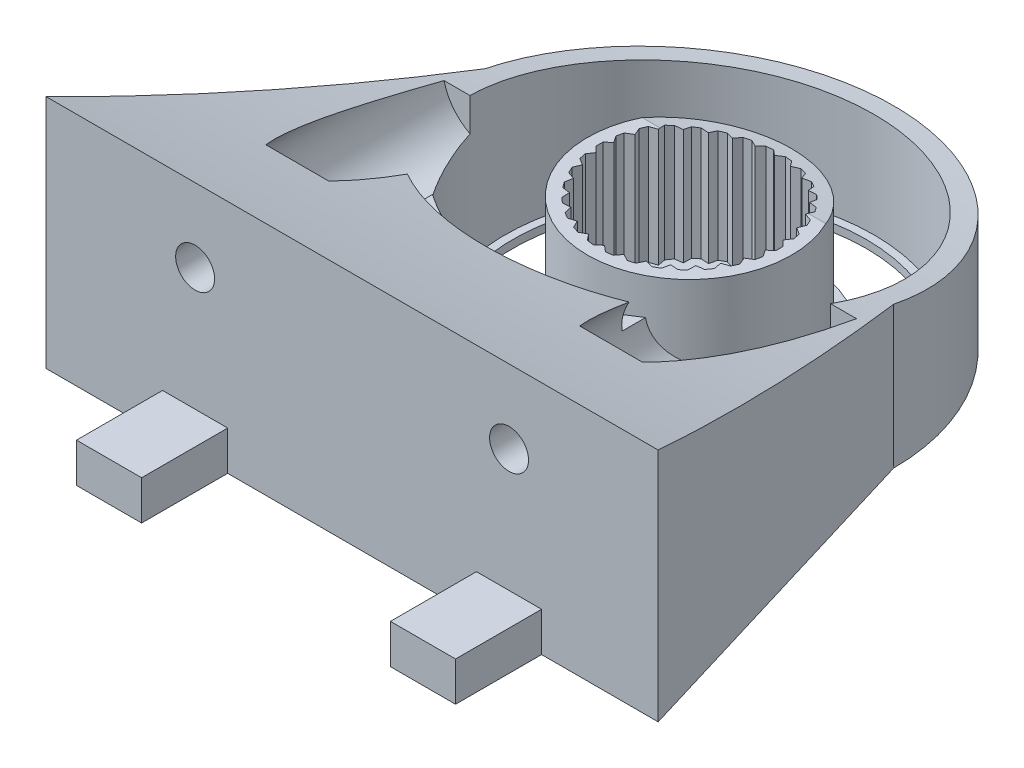
SolidWorks part; units mm, degrees
ref_plane "Front Plane" through (0, 0, 0) normal (0, 0, 1) x (1, 0, 0)
ref_plane "Top Plane" through (0, 0, 0) normal (0, 1, 0) x (1, 0, 0)
ref_plane "Right Plane" through (0, 0, 0) normal (1, 0, 0) x (0, 0, -1)
sketch "Sketch1" plane through (0, 0, 0) normal (0, 1, 0) x (1, 0, 0)
  line L208 (0, 27.1182) -> (0, 42.0182) construction
  line L209 (0, 57.7182) -> (-47.2537, 57.7182) construction
  line L210 (16.6412, 0.931) -> (17.2272, 1.5169) construction
  line L211 (14.3988, 4.3454) -> (13.8128, 3.7594) construction
  line L212 (13.8128, 10.4769) -> (14.3988, 9.891) construction
  line L213 (17.2272, 12.7194) -> (16.6412, 13.3054) construction
  line L214 (23.3588, 13.3054) -> (22.7728, 12.7194) construction
  line L215 (25.6012, 9.891) -> (26.1872, 10.4769) construction
  line L216 (26.1872, 3.7594) -> (25.6012, 4.3454) construction
  line L217 (22.7728, 1.5169) -> (23.3588, 0.931) construction
  line L218 (-29.6, -20.9818) -> (-29.6, -4.7818) construction
  line L219 (-38, -20.9818) -> (-29.6, -20.9818) construction
  line L220 (-38, -4.7818) -> (-38, -20.9818) construction
  line L221 (-29.6, -4.7818) -> (-38, -4.7818) construction
  line L222 (-23.3588, 0.931) -> (-22.7728, 1.5169) construction
  line L223 (-25.6012, 4.3454) -> (-26.1872, 3.7594) construction
  line L224 (-26.1872, 10.4769) -> (-25.6012, 9.891) construction
  line L225 (-22.7728, 12.7194) -> (-23.3588, 13.3054) construction
  line L226 (-16.6412, 13.3054) -> (-17.2272, 12.7194) construction
  line L227 (-14.3988, 9.891) -> (-13.8128, 10.4769) construction
  line L228 (-13.8128, 3.7594) -> (-14.3988, 4.3454) construction
  line L229 (-17.2272, 1.5169) -> (-16.6412, 0.931) construction
  line L230 (23.3588, -26.6946) -> (22.7728, -27.2806) construction
  line L231 (25.6012, -30.109) -> (26.1872, -29.5231) construction
  line L232 (26.1872, -36.2406) -> (25.6012, -35.6546) construction
  line L233 (22.7728, -38.4831) -> (23.3588, -39.069) construction
  line L234 (16.6412, -39.069) -> (17.2272, -38.4831) construction
  line L235 (14.3988, -35.6546) -> (13.8128, -36.2406) construction
  line L236 (13.8128, -29.5231) -> (14.3988, -30.109) construction
  line L237 (17.2272, -27.2806) -> (16.6412, -26.6946) construction
  line L238 (-31.2, -44.0818) -> (-38.4, -44.0818) construction
  line L239 (-31.2, -51.2818) -> (-31.2, -44.0818) construction
  line L240 (-38.4, -51.2818) -> (-31.2, -51.2818) construction
  line L241 (-38.4, -44.0818) -> (-38.4, -51.2818) construction
  line L242 (-16.6412, -26.6946) -> (-17.2272, -27.2806) construction
  line L243 (-14.3988, -30.109) -> (-13.8128, -29.5231) construction
  line L244 (-13.8128, -36.2406) -> (-14.3988, -35.6546) construction
  line L245 (-17.2272, -38.4831) -> (-16.6412, -39.069) construction
  line L246 (-23.3588, -39.069) -> (-22.7728, -38.4831) construction
  line L247 (-25.6012, -35.6546) -> (-26.1872, -36.2406) construction
  line L248 (-26.1872, -29.5231) -> (-25.6012, -30.109) construction
  line L249 (-22.7728, -27.2806) -> (-23.3588, -26.6946) construction
  line L250 (-38.4, 18.3182) -> (-31.2, 18.3182) construction
  line L251 (-38.4, 25.5182) -> (-38.4, 18.3182) construction
  line L252 (-31.2, 25.5182) -> (-38.4, 25.5182) construction
  line L253 (-31.2, 18.3182) -> (-31.2, 25.5182) construction
  line L254 (38.4, -44.0818) -> (31.2, -44.0818) construction
  line L255 (38.4, -51.2818) -> (38.4, -44.0818) construction
  line L256 (31.2, -51.2818) -> (38.4, -51.2818) construction
  line L257 (31.2, -44.0818) -> (31.2, -51.2818) construction
  line L258 (31.2, 18.3182) -> (38.4, 18.3182) construction
  line L259 (31.2, 25.5182) -> (31.2, 18.3182) construction
  line L260 (38.4, 25.5182) -> (31.2, 25.5182) construction
  line L261 (38.4, 18.3182) -> (38.4, 25.5182) construction
  line L262 (-8.1, 25.1182) -> (-8.1, 16.7182) construction
  line L263 (8.1, 25.1182) -> (-8.1, 25.1182) construction
  line L264 (8.1, 16.7182) -> (8.1, 25.1182) construction
  line L265 (-8.1, 16.7182) -> (8.1, 16.7182) construction
  line L266 (11.2, -37.6818) -> (11.2, -28.0818) construction
  line L267 (-9.2, -39.6818) -> (9.2, -39.6818) construction
  line L268 (-11.2, -28.0818) -> (-11.2, -37.6818) construction
  line L269 (-24.8, -24.0818) -> (-15.2, -24.0818) construction
  line L270 (-26.8, -3.6818) -> (-26.8, -22.0818) construction
  line L271 (-15.2, -1.6818) -> (-24.8, -1.6818) construction
  line L272 (-11.2, 11.9182) -> (-11.2, 2.3182) construction
  line L273 (9.2, 13.9182) -> (-9.2, 13.9182) construction
  line L274 (11.2, 2.3182) -> (11.2, 11.9182) construction
  line L275 (24.8, -1.6818) -> (15.2, -1.6818) construction
  line L276 (26.8, -22.0818) -> (26.8, -3.6818) construction
  line L277 (15.2, -24.0818) -> (24.8, -24.0818) construction
  line L278 (8.1, -42.4818) -> (-8.1, -42.4818) construction
  line L279 (8.1, -50.8818) -> (8.1, -42.4818) construction
  line L280 (-8.1, -50.8818) -> (8.1, -50.8818) construction
  line L281 (-8.1, -42.4818) -> (-8.1, -50.8818) construction
  line L282 (29.6, -4.7818) -> (29.6, -20.9818) construction
  line L283 (38, -4.7818) -> (29.6, -4.7818) construction
  line L284 (38, -20.9818) -> (38, -4.7818) construction
  line L285 (29.6, -20.9818) -> (38, -20.9818) construction
  line L286 (40, -51.8818) -> (40, -38.1318) construction
  line L287 (40, -38.1318) -> (39, -37.1318) construction
  line L288 (39, -37.1318) -> (36, -37.1318) construction
  line L289 (36, -37.1318) -> (36, -40.1318) construction
  line L290 (36, -40.1318) -> (37.6041, -40.1318) construction
  line L291 (38.0965, -40.7186) -> (37.9168, -41.7381) construction
  line L292 (37.0304, -42.4818) -> (32.3339, -42.4818) construction
  line L293 (30.2125, -41.6031) -> (29.6787, -41.0693) construction
  line L294 (28.8, -38.9479) -> (28.8, -26.8157) construction
  line L295 (29.6787, -24.6944) -> (30.2125, -24.1605) construction
  line L296 (32.3339, -23.2818) -> (37.0304, -23.2818) construction
  line L297 (37.9168, -24.0255) -> (38.0965, -25.045) construction
  line L298 (37.6041, -25.6318) -> (36, -25.6318) construction
  line L299 (36, -25.6318) -> (36, -28.6318) construction
  line L300 (36, -28.6318) -> (39, -28.6318) construction
  line L301 (39, -28.6318) -> (40, -27.6318) construction
  line L302 (40, -27.6318) -> (40, 1.8682) construction
  line L303 (40, 1.8682) -> (39, 2.8682) construction
  line L304 (39, 2.8682) -> (36, 2.8682) construction
  line L305 (36, 2.8682) -> (36, -0.1318) construction
  line L306 (36, -0.1318) -> (37.6041, -0.1318) construction
  line L307 (38.0965, -0.7186) -> (37.9168, -1.7381) construction
  line L308 (37.0304, -2.4818) -> (32.3339, -2.4818) construction
  line L309 (30.2125, -1.6031) -> (29.6787, -1.0693) construction
  line L310 (28.8, 1.0521) -> (28.8, 13.1843) construction
  line L311 (29.6787, 15.3056) -> (30.2125, 15.8395) construction
  line L312 (32.3339, 16.7182) -> (37.0304, 16.7182) construction
  line L313 (37.9168, 15.9745) -> (38.0965, 14.955) construction
  line L314 (37.6041, 14.3682) -> (36, 14.3682) construction
  line L315 (36, 14.3682) -> (36, 11.3682) construction
  line L316 (36, 11.3682) -> (39, 11.3682) construction
  line L317 (39, 11.3682) -> (40, 12.3682) construction
  line L318 (40, 12.3682) -> (40, 26.1182) construction
  line L319 (39, 27.1182) -> (25.25, 27.1182) construction
  line L320 (25.25, 27.1182) -> (24.25, 26.1182) construction
  line L321 (24.25, 26.1182) -> (24.25, 23.1182) construction
  line L322 (24.25, 23.1182) -> (27.25, 23.1182) construction
  line L323 (27.25, 23.1182) -> (27.25, 24.7223) construction
  line L324 (27.8368, 25.2147) -> (28.8563, 25.035) construction
  line L325 (29.6, 24.1486) -> (29.6, 19.4521) construction
  line L326 (28.7213, 17.3307) -> (28.1875, 16.7969) construction
  line L327 (26.0661, 15.9182) -> (13.9339, 15.9182) construction
  line L328 (11.8125, 16.7969) -> (11.2787, 17.3307) construction
  line L329 (10.4, 19.4521) -> (10.4, 24.1486) construction
  line L330 (11.1437, 25.035) -> (12.1632, 25.2147) construction
  line L331 (12.75, 24.7223) -> (12.75, 23.1182) construction
  line L332 (12.75, 23.1182) -> (15.75, 23.1182) construction
  line L333 (15.75, 23.1182) -> (15.75, 26.1182) construction
  line L334 (15.75, 26.1182) -> (14.75, 27.1182) construction
  line L335 (14.75, 27.1182) -> (-14.75, 27.1182) construction
  line L336 (-14.75, 27.1182) -> (-15.75, 26.1182) construction
  line L337 (-15.75, 26.1182) -> (-15.75, 23.1182) construction
  line L338 (-15.75, 23.1182) -> (-12.75, 23.1182) construction
  line L339 (-12.75, 23.1182) -> (-12.75, 24.7223) construction
  line L340 (-12.1632, 25.2147) -> (-11.1437, 25.035) construction
  line L341 (-10.4, 24.1486) -> (-10.4, 19.4521) construction
  line L342 (-11.2787, 17.3307) -> (-11.8125, 16.7969) construction
  line L343 (-13.9339, 15.9182) -> (-26.0661, 15.9182) construction
  line L344 (-28.1875, 16.7969) -> (-28.7213, 17.3307) construction
  line L345 (-29.6, 19.4521) -> (-29.6, 24.1486) construction
  line L346 (-28.8563, 25.035) -> (-27.8368, 25.2147) construction
  line L347 (-27.25, 24.7223) -> (-27.25, 23.1182) construction
  line L348 (-27.25, 23.1182) -> (-24.25, 23.1182) construction
  line L349 (-24.25, 23.1182) -> (-24.25, 26.1182) construction
  line L350 (-24.25, 26.1182) -> (-25.25, 27.1182) construction
  line L351 (-25.25, 27.1182) -> (-39, 27.1182) construction
  line L352 (-40, 26.1182) -> (-40, 12.3682) construction
  line L353 (-40, 12.3682) -> (-39, 11.3682) construction
  line L354 (-39, 11.3682) -> (-36, 11.3682) construction
  line L355 (-36, 11.3682) -> (-36, 14.3682) construction
  line L356 (-36, 14.3682) -> (-37.6041, 14.3682) construction
  line L357 (-38.0965, 14.955) -> (-37.9168, 15.9745) construction
  line L358 (-37.0304, 16.7182) -> (-32.3339, 16.7182) construction
  line L359 (-30.2125, 15.8395) -> (-29.6787, 15.3056) construction
  line L360 (-28.8, 13.1843) -> (-28.8, 1.0521) construction
  line L361 (-29.6787, -1.0693) -> (-30.2125, -1.6031) construction
  line L362 (-32.3339, -2.4818) -> (-37.0304, -2.4818) construction
  line L363 (-37.9168, -1.7381) -> (-38.0965, -0.7186) construction
  line L364 (-37.6041, -0.1318) -> (-36, -0.1318) construction
  line L365 (-36, -0.1318) -> (-36, 2.8682) construction
  line L366 (-36, 2.8682) -> (-39, 2.8682) construction
  line L367 (-39, 2.8682) -> (-40, 1.8682) construction
  line L368 (-40, 1.8682) -> (-40, -27.6318) construction
  line L369 (-40, -27.6318) -> (-39, -28.6318) construction
  line L370 (-39, -28.6318) -> (-36, -28.6318) construction
  line L371 (-36, -28.6318) -> (-36, -25.6318) construction
  line L372 (-36, -25.6318) -> (-37.6041, -25.6318) construction
  line L373 (-38.0965, -25.045) -> (-37.9168, -24.0255) construction
  line L374 (-37.0304, -23.2818) -> (-32.3339, -23.2818) construction
  line L375 (-30.2125, -24.1605) -> (-29.6787, -24.6944) construction
  line L376 (-28.8, -26.8157) -> (-28.8, -38.9479) construction
  line L377 (-29.6787, -41.0693) -> (-30.2125, -41.6031) construction
  line L378 (-32.3339, -42.4818) -> (-37.0304, -42.4818) construction
  line L379 (-37.9168, -41.7381) -> (-38.0965, -40.7186) construction
  line L380 (-37.6041, -40.1318) -> (-36, -40.1318) construction
  line L381 (-36, -40.1318) -> (-36, -37.1318) construction
  line L382 (-36, -37.1318) -> (-39, -37.1318) construction
  line L383 (-39, -37.1318) -> (-40, -38.1318) construction
  line L384 (-40, -38.1318) -> (-40, -51.8818) construction
  line L385 (-39, -52.8818) -> (-25.25, -52.8818) construction
  line L386 (-25.25, -52.8818) -> (-24.25, -51.8818) construction
  line L387 (-24.25, -51.8818) -> (-24.25, -48.8818) construction
  line L388 (-24.25, -48.8818) -> (-27.25, -48.8818) construction
  line L389 (-27.25, -48.8818) -> (-27.25, -50.4859) construction
  line L390 (-27.8368, -50.9783) -> (-28.8563, -50.7986) construction
  line L391 (-29.6, -49.9123) -> (-29.6, -45.2157) construction
  line L392 (-28.7213, -43.0944) -> (-28.1875, -42.5605) construction
  line L393 (-26.0661, -41.6818) -> (-13.9339, -41.6818) construction
  line L394 (-11.8125, -42.5605) -> (-11.2787, -43.0944) construction
  line L395 (-10.4, -45.2157) -> (-10.4, -49.9123) construction
  line L396 (-11.1437, -50.7986) -> (-12.1632, -50.9783) construction
  line L397 (-12.75, -50.4859) -> (-12.75, -48.8818) construction
  line L398 (-12.75, -48.8818) -> (-15.75, -48.8818) construction
  line L399 (-15.75, -48.8818) -> (-15.75, -51.8818) construction
  line L400 (-15.75, -51.8818) -> (-14.75, -52.8818) construction
  line L401 (-14.75, -52.8818) -> (14.75, -52.8818) construction
  line L402 (14.75, -52.8818) -> (15.75, -51.8818) construction
  line L403 (15.75, -51.8818) -> (15.75, -48.8818) construction
  line L404 (15.75, -48.8818) -> (12.75, -48.8818) construction
  line L405 (12.75, -48.8818) -> (12.75, -50.4859) construction
  line L406 (12.1632, -50.9783) -> (11.1437, -50.7986) construction
  line L407 (10.4, -49.9123) -> (10.4, -45.2157) construction
  line L408 (11.2787, -43.0944) -> (11.8125, -42.5605) construction
  line L409 (13.9339, -41.6818) -> (26.0661, -41.6818) construction
  line L410 (28.1875, -42.5605) -> (28.7213, -43.0944) construction
  line L411 (29.6, -45.2157) -> (29.6, -49.9123) construction
  line L412 (28.8563, -50.7986) -> (27.8368, -50.9783) construction
  line L413 (27.25, -50.4859) -> (27.25, -48.8818) construction
  line L414 (27.25, -48.8818) -> (24.25, -48.8818) construction
  line L415 (24.25, -48.8818) -> (24.25, -51.8818) construction
  line L416 (24.25, -51.8818) -> (25.25, -52.8818) construction
  line L417 (25.25, -52.8818) -> (39, -52.8818) construction
  line L418 (0, 82.2765) -> (0, 80.95) construction
  line L419 (0, 80.95) -> (-0.7581, 81.5932)
  line L420 (0, 80.95) -> (0.7581, 81.5932)
  line L421 (2.2521, 80.7133) -> (1.6443, 81.5)
  line L422 (2.2521, 80.7133) -> (3.1273, 81.1848)
  line L423 (4.4057, 80.0136) -> (3.9748, 80.9094)
  line L424 (4.4057, 80.0136) -> (5.3598, 80.2928)
  line L425 (6.3668, 78.8813) -> (6.1315, 79.8472)
  line L426 (6.3668, 78.8813) -> (7.3581, 78.9561)
  line L427 (8.0496, 77.3661) -> (8.0203, 78.3598)
  line L428 (8.0496, 77.3661) -> (9.0348, 77.2331)
  line L429 (9.3806, 75.5341) -> (9.5586, 76.5122)
  line L430 (9.3806, 75.5341) -> (10.3167, 75.1992)
  line L431 (10.3017, 73.4654) -> (10.6791, 74.3851)
  line L432 (10.3017, 73.4654) -> (11.1476, 72.9432)
  line L433 (10.7725, 71.2504) -> (11.3329, 72.0716)
  line L434 (10.7725, 71.2504) -> (11.4914, 70.5637)
  line L435 (10.7725, 68.986) -> (11.4914, 69.6726)
  line L436 (10.7725, 68.986) -> (11.3329, 68.1648)
  line L437 (10.3017, 66.771) -> (11.1476, 67.2932)
  line L438 (10.3017, 66.771) -> (10.6791, 65.8513)
  line L439 (9.3806, 64.7023) -> (10.3167, 65.0372)
  line L440 (9.3806, 64.7023) -> (9.5586, 63.7242)
  line L441 (8.0496, 62.8703) -> (9.0348, 63.0033)
  line L442 (8.0496, 62.8703) -> (8.0203, 61.8766)
  line L443 (6.3668, 61.3551) -> (7.3581, 61.2803)
  line L444 (6.3668, 61.3551) -> (6.1315, 60.3891)
  line L445 (4.4057, 60.2228) -> (5.3598, 59.9436)
  line L446 (4.4057, 60.2228) -> (3.9748, 59.3269)
  line L447 (2.2521, 59.5231) -> (3.1273, 59.0516)
  line L448 (2.2521, 59.5231) -> (1.6443, 58.7363)
  line L449 (0, 59.2864) -> (0.7581, 58.6432)
  line L450 (0, 59.2864) -> (-0.7581, 58.6432)
  line L451 (-2.2521, 59.5231) -> (-1.6443, 58.7363)
  line L452 (-2.2521, 59.5231) -> (-3.1273, 59.0516)
  line L453 (-4.4057, 60.2228) -> (-3.9748, 59.3269)
  line L454 (-4.4057, 60.2228) -> (-5.3598, 59.9436)
  line L455 (-6.3668, 61.3551) -> (-6.1315, 60.3891)
  line L456 (-6.3668, 61.3551) -> (-7.3581, 61.2803)
  line L457 (-8.0496, 62.8703) -> (-8.0203, 61.8766)
  line L458 (-8.0496, 62.8703) -> (-9.0348, 63.0033)
  line L459 (-9.3806, 64.7023) -> (-9.5586, 63.7242)
  line L460 (-9.3806, 64.7023) -> (-10.3167, 65.0372)
  line L461 (-10.3017, 66.771) -> (-10.6791, 65.8513)
  line L462 (-10.3017, 66.771) -> (-11.1476, 67.2932)
  line L463 (-10.7725, 68.986) -> (-11.3329, 68.1648)
  line L464 (-10.7725, 68.986) -> (-11.4914, 69.6726)
  line L465 (-10.7725, 71.2504) -> (-11.4914, 70.5637)
  line L466 (-10.7725, 71.2504) -> (-11.3329, 72.0716)
  line L467 (-10.3017, 73.4654) -> (-11.1476, 72.9432)
  line L468 (-10.3017, 73.4654) -> (-10.6791, 74.3851)
  line L469 (-9.3806, 75.5341) -> (-10.3167, 75.1992)
  line L470 (-9.3806, 75.5341) -> (-9.5586, 76.5122)
  line L471 (-8.0496, 77.3661) -> (-9.0348, 77.2331)
  line L472 (-8.0496, 77.3661) -> (-8.0203, 78.3598)
  line L473 (-6.3668, 78.8813) -> (-7.3581, 78.9561)
  line L474 (-6.3668, 78.8813) -> (-6.1315, 79.8472)
  line L475 (-4.4057, 80.0136) -> (-5.3598, 80.2928)
  line L476 (-4.4057, 80.0136) -> (-3.9748, 80.9094)
  line L477 (-2.2521, 80.7133) -> (-3.1273, 81.1848)
  line L478 (-2.2521, 80.7133) -> (-1.6443, 81.5)
  line L479 (0, 57.1182) -> (0, 70.1182) construction
  circle A112 centre (0, 70.1182) radius 12.4 construction
  circle A114 centre (0, 70.1182) radius 13
  arc A121 (17.2272, 1.5169) -> (22.7728, 1.5169) centre (20, 7.1182) ccw construction
  arc A122 (13.8128, 3.7594) -> (16.6412, 0.931) centre (15.227, 2.3452) ccw construction
  arc A123 (14.3988, 9.891) -> (14.3988, 4.3454) centre (20, 7.1182) ccw construction
  arc A124 (16.6412, 13.3054) -> (13.8128, 10.4769) centre (15.227, 11.8912) ccw construction
  arc A125 (22.7728, 12.7194) -> (17.2272, 12.7194) centre (20, 7.1182) ccw construction
  arc A126 (26.1872, 10.4769) -> (23.3588, 13.3054) centre (24.773, 11.8912) ccw construction
  arc A127 (25.6012, 4.3454) -> (25.6012, 9.891) centre (20, 7.1182) ccw construction
  arc A128 (23.3588, 0.931) -> (26.1872, 3.7594) centre (24.773, 2.3452) ccw construction
  arc A129 (-22.7728, 1.5169) -> (-17.2272, 1.5169) centre (-20, 7.1182) ccw construction
  arc A130 (-26.1872, 3.7594) -> (-23.3588, 0.931) centre (-24.773, 2.3452) ccw construction
  arc A131 (-25.6012, 9.891) -> (-25.6012, 4.3454) centre (-20, 7.1182) ccw construction
  arc A132 (-23.3588, 13.3054) -> (-26.1872, 10.4769) centre (-24.773, 11.8912) ccw construction
  arc A133 (-17.2272, 12.7194) -> (-22.7728, 12.7194) centre (-20, 7.1182) ccw construction
  arc A134 (-13.8128, 10.4769) -> (-16.6412, 13.3054) centre (-15.227, 11.8912) ccw construction
  arc A135 (-14.3988, 4.3454) -> (-14.3988, 9.891) centre (-20, 7.1182) ccw construction
  arc A136 (-16.6412, 0.931) -> (-13.8128, 3.7594) centre (-15.227, 2.3452) ccw construction
  arc A137 (22.7728, -27.2806) -> (17.2272, -27.2806) centre (20, -32.8818) ccw construction
  arc A138 (26.1872, -29.5231) -> (23.3588, -26.6946) centre (24.773, -28.1088) ccw construction
  arc A139 (25.6012, -35.6546) -> (25.6012, -30.109) centre (20, -32.8818) ccw construction
  arc A140 (23.3588, -39.069) -> (26.1872, -36.2406) centre (24.773, -37.6548) ccw construction
  arc A141 (17.2272, -38.4831) -> (22.7728, -38.4831) centre (20, -32.8818) ccw construction
  arc A142 (13.8128, -36.2406) -> (16.6412, -39.069) centre (15.227, -37.6548) ccw construction
  arc A143 (14.3988, -30.109) -> (14.3988, -35.6546) centre (20, -32.8818) ccw construction
  arc A144 (16.6412, -26.6946) -> (13.8128, -29.5231) centre (15.227, -28.1088) ccw construction
  arc A145 (-17.2272, -27.2806) -> (-22.7728, -27.2806) centre (-20, -32.8818) ccw construction
  arc A146 (-13.8128, -29.5231) -> (-16.6412, -26.6946) centre (-15.227, -28.1088) ccw construction
  arc A147 (-14.3988, -35.6546) -> (-14.3988, -30.109) centre (-20, -32.8818) ccw construction
  arc A148 (-16.6412, -39.069) -> (-13.8128, -36.2406) centre (-15.227, -37.6548) ccw construction
  arc A149 (-22.7728, -38.4831) -> (-17.2272, -38.4831) centre (-20, -32.8818) ccw construction
  arc A150 (-26.1872, -36.2406) -> (-23.3588, -39.069) centre (-24.773, -37.6548) ccw construction
  arc A151 (-25.6012, -30.109) -> (-25.6012, -35.6546) centre (-20, -32.8818) ccw construction
  arc A152 (-23.3588, -26.6946) -> (-26.1872, -29.5231) centre (-24.773, -28.1088) ccw construction
  arc A153 (15.2, -24.0818) -> (11.2, -28.0818) centre (15.2, -28.0818) ccw construction
  arc A154 (9.2, -39.6818) -> (11.2, -37.6818) centre (9.2, -37.6818) ccw construction
  arc A155 (-11.2, -37.6818) -> (-9.2, -39.6818) centre (-9.2, -37.6818) ccw construction
  arc A156 (-11.2, -28.0818) -> (-15.2, -24.0818) centre (-15.2, -28.0818) ccw construction
  arc A157 (-26.8, -22.0818) -> (-24.8, -24.0818) centre (-24.8, -22.0818) ccw construction
  arc A158 (-24.8, -1.6818) -> (-26.8, -3.6818) centre (-24.8, -3.6818) ccw construction
  arc A159 (-15.2, -1.6818) -> (-11.2, 2.3182) centre (-15.2, 2.3182) ccw construction
  arc A160 (-9.2, 13.9182) -> (-11.2, 11.9182) centre (-9.2, 11.9182) ccw construction
  arc A161 (11.2, 11.9182) -> (9.2, 13.9182) centre (9.2, 11.9182) ccw construction
  arc A162 (11.2, 2.3182) -> (15.2, -1.6818) centre (15.2, 2.3182) ccw construction
  arc A163 (26.8, -3.6818) -> (24.8, -1.6818) centre (24.8, -3.6818) ccw construction
  arc A164 (24.8, -24.0818) -> (26.8, -22.0818) centre (24.8, -22.0818) ccw construction
  arc A165 (39, -52.8818) -> (40, -51.8818) centre (39, -51.8818) ccw construction
  arc A166 (38.0965, -40.7186) -> (37.6041, -40.1318) centre (37.6041, -40.6318) ccw construction
  arc A167 (37.0304, -42.4818) -> (37.9168, -41.7381) centre (37.0304, -41.5818) ccw construction
  arc A168 (30.2125, -41.6031) -> (32.3339, -42.4818) centre (32.3339, -39.4818) ccw construction
  arc A169 (28.8, -38.9479) -> (29.6787, -41.0693) centre (31.8, -38.9479) ccw construction
  arc A170 (29.6787, -24.6944) -> (28.8, -26.8157) centre (31.8, -26.8157) ccw construction
  arc A171 (32.3339, -23.2818) -> (30.2125, -24.1605) centre (32.3339, -26.2818) ccw construction
  arc A172 (37.9168, -24.0255) -> (37.0304, -23.2818) centre (37.0304, -24.1818) ccw construction
  arc A173 (37.6041, -25.6318) -> (38.0965, -25.045) centre (37.6041, -25.1318) ccw construction
  arc A174 (38.0965, -0.7186) -> (37.6041, -0.1318) centre (37.6041, -0.6318) ccw construction
  arc A175 (37.0304, -2.4818) -> (37.9168, -1.7381) centre (37.0304, -1.5818) ccw construction
  arc A176 (30.2125, -1.6031) -> (32.3339, -2.4818) centre (32.3339, 0.5182) ccw construction
  arc A177 (28.8, 1.0521) -> (29.6787, -1.0693) centre (31.8, 1.0521) ccw construction
  arc A178 (29.6787, 15.3056) -> (28.8, 13.1843) centre (31.8, 13.1843) ccw construction
  arc A179 (32.3339, 16.7182) -> (30.2125, 15.8395) centre (32.3339, 13.7182) ccw construction
  arc A180 (37.9168, 15.9745) -> (37.0304, 16.7182) centre (37.0304, 15.8182) ccw construction
  arc A181 (37.6041, 14.3682) -> (38.0965, 14.955) centre (37.6041, 14.8682) ccw construction
  arc A182 (40, 26.1182) -> (39, 27.1182) centre (39, 26.1182) ccw construction
  arc A183 (27.8368, 25.2147) -> (27.25, 24.7223) centre (27.75, 24.7223) ccw construction
  arc A184 (29.6, 24.1486) -> (28.8563, 25.035) centre (28.7, 24.1486) ccw construction
  arc A185 (28.7213, 17.3307) -> (29.6, 19.4521) centre (26.6, 19.4521) ccw construction
  arc A186 (26.0661, 15.9182) -> (28.1875, 16.7969) centre (26.0661, 18.9182) ccw construction
  arc A187 (11.8125, 16.7969) -> (13.9339, 15.9182) centre (13.9339, 18.9182) ccw construction
  arc A188 (10.4, 19.4521) -> (11.2787, 17.3307) centre (13.4, 19.4521) ccw construction
  arc A189 (11.1437, 25.035) -> (10.4, 24.1486) centre (11.3, 24.1486) ccw construction
  arc A190 (12.75, 24.7223) -> (12.1632, 25.2147) centre (12.25, 24.7223) ccw construction
  arc A191 (-12.1632, 25.2147) -> (-12.75, 24.7223) centre (-12.25, 24.7223) ccw construction
  arc A192 (-10.4, 24.1486) -> (-11.1437, 25.035) centre (-11.3, 24.1486) ccw construction
  arc A193 (-11.2787, 17.3307) -> (-10.4, 19.4521) centre (-13.4, 19.4521) ccw construction
  arc A194 (-13.9339, 15.9182) -> (-11.8125, 16.7969) centre (-13.9339, 18.9182) ccw construction
  arc A195 (-28.1875, 16.7969) -> (-26.0661, 15.9182) centre (-26.0661, 18.9182) ccw construction
  arc A196 (-29.6, 19.4521) -> (-28.7213, 17.3307) centre (-26.6, 19.4521) ccw construction
  arc A197 (-28.8563, 25.035) -> (-29.6, 24.1486) centre (-28.7, 24.1486) ccw construction
  arc A198 (-27.25, 24.7223) -> (-27.8368, 25.2147) centre (-27.75, 24.7223) ccw construction
  arc A199 (-39, 27.1182) -> (-40, 26.1182) centre (-39, 26.1182) ccw construction
  arc A200 (-38.0965, 14.955) -> (-37.6041, 14.3682) centre (-37.6041, 14.8682) ccw construction
  arc A201 (-37.0304, 16.7182) -> (-37.9168, 15.9745) centre (-37.0304, 15.8182) ccw construction
  arc A202 (-30.2125, 15.8395) -> (-32.3339, 16.7182) centre (-32.3339, 13.7182) ccw construction
  arc A203 (-28.8, 13.1843) -> (-29.6787, 15.3056) centre (-31.8, 13.1843) ccw construction
  arc A204 (-29.6787, -1.0693) -> (-28.8, 1.0521) centre (-31.8, 1.0521) ccw construction
  arc A205 (-32.3339, -2.4818) -> (-30.2125, -1.6031) centre (-32.3339, 0.5182) ccw construction
  arc A206 (-37.9168, -1.7381) -> (-37.0304, -2.4818) centre (-37.0304, -1.5818) ccw construction
  arc A207 (-37.6041, -0.1318) -> (-38.0965, -0.7186) centre (-37.6041, -0.6318) ccw construction
  arc A208 (-38.0965, -25.045) -> (-37.6041, -25.6318) centre (-37.6041, -25.1318) ccw construction
  arc A209 (-37.0304, -23.2818) -> (-37.9168, -24.0255) centre (-37.0304, -24.1818) ccw construction
  arc A210 (-30.2125, -24.1605) -> (-32.3339, -23.2818) centre (-32.3339, -26.2818) ccw construction
  arc A211 (-28.8, -26.8157) -> (-29.6787, -24.6944) centre (-31.8, -26.8157) ccw construction
  arc A212 (-29.6787, -41.0693) -> (-28.8, -38.9479) centre (-31.8, -38.9479) ccw construction
  arc A213 (-32.3339, -42.4818) -> (-30.2125, -41.6031) centre (-32.3339, -39.4818) ccw construction
  arc A214 (-37.9168, -41.7381) -> (-37.0304, -42.4818) centre (-37.0304, -41.5818) ccw construction
  arc A215 (-37.6041, -40.1318) -> (-38.0965, -40.7186) centre (-37.6041, -40.6318) ccw construction
  arc A216 (-40, -51.8818) -> (-39, -52.8818) centre (-39, -51.8818) ccw construction
  arc A217 (-27.8368, -50.9783) -> (-27.25, -50.4859) centre (-27.75, -50.4859) ccw construction
  arc A218 (-29.6, -49.9123) -> (-28.8563, -50.7986) centre (-28.7, -49.9123) ccw construction
  arc A219 (-28.7213, -43.0944) -> (-29.6, -45.2157) centre (-26.6, -45.2157) ccw construction
  arc A220 (-26.0661, -41.6818) -> (-28.1875, -42.5605) centre (-26.0661, -44.6818) ccw construction
  arc A221 (-11.8125, -42.5605) -> (-13.9339, -41.6818) centre (-13.9339, -44.6818) ccw construction
  arc A222 (-10.4, -45.2157) -> (-11.2787, -43.0944) centre (-13.4, -45.2157) ccw construction
  arc A223 (-11.1437, -50.7986) -> (-10.4, -49.9123) centre (-11.3, -49.9123) ccw construction
  arc A224 (-12.75, -50.4859) -> (-12.1632, -50.9783) centre (-12.25, -50.4859) ccw construction
  arc A225 (12.1632, -50.9783) -> (12.75, -50.4859) centre (12.25, -50.4859) ccw construction
  arc A226 (10.4, -49.9123) -> (11.1437, -50.7986) centre (11.3, -49.9123) ccw construction
  arc A227 (11.2787, -43.0944) -> (10.4, -45.2157) centre (13.4, -45.2157) ccw construction
  arc A228 (13.9339, -41.6818) -> (11.8125, -42.5605) centre (13.9339, -44.6818) ccw construction
  arc A229 (28.1875, -42.5605) -> (26.0661, -41.6818) centre (26.0661, -44.6818) ccw construction
  arc A230 (29.6, -45.2157) -> (28.7213, -43.0944) centre (26.6, -45.2157) ccw construction
  arc A231 (28.8563, -50.7986) -> (29.6, -49.9123) centre (28.7, -49.9123) ccw construction
  arc A232 (27.25, -50.4859) -> (27.8368, -50.9783) centre (27.75, -50.4859) ccw construction
  arc A233 (-9.0348, 77.2331) -> (-9.5586, 76.5122) centre (0, 70.1182) ccw
  arc A234 (-7.3581, 78.9561) -> (-8.0203, 78.3598) centre (0, 70.1182) ccw
  arc A235 (-5.3598, 80.2928) -> (-6.1315, 79.8472) centre (0, 70.1182) ccw
  arc A236 (-3.1273, 81.1848) -> (-3.9748, 80.9094) centre (0, 70.1182) ccw
  arc A237 (-0.7581, 81.5932) -> (-1.6443, 81.5) centre (0, 70.1182) ccw
  arc A238 (1.6443, 81.5) -> (0.7581, 81.5932) centre (0, 70.1182) ccw
  arc A239 (3.9748, 80.9094) -> (3.1273, 81.1848) centre (0, 70.1182) ccw
  arc A240 (6.1315, 79.8472) -> (5.3598, 80.2928) centre (0, 70.1182) ccw
  arc A241 (8.0203, 78.3598) -> (7.3581, 78.9561) centre (0, 70.1182) ccw
  arc A242 (9.5586, 76.5122) -> (9.0348, 77.2331) centre (0, 70.1182) ccw
  arc A243 (10.6791, 74.3851) -> (10.3167, 75.1992) centre (0, 70.1182) ccw
  arc A244 (11.3329, 72.0716) -> (11.1476, 72.9432) centre (0, 70.1182) ccw
  arc A245 (11.4914, 69.6726) -> (11.4914, 70.5637) centre (0, 70.1182) ccw
  arc A246 (11.1476, 67.2932) -> (11.3329, 68.1648) centre (0, 70.1182) ccw
  arc A247 (-10.3167, 75.1992) -> (-10.6791, 74.3851) centre (0, 70.1182) ccw
  arc A248 (-11.1476, 72.9432) -> (-11.3329, 72.0716) centre (0, 70.1182) ccw
  arc A249 (-11.4914, 70.5637) -> (-11.4914, 69.6726) centre (0, 70.1182) ccw
  arc A250 (-11.3329, 68.1648) -> (-11.1476, 67.2932) centre (0, 70.1182) ccw
  arc A251 (-10.6791, 65.8513) -> (-10.3167, 65.0372) centre (0, 70.1182) ccw
  arc A252 (-9.5586, 63.7242) -> (-9.0348, 63.0033) centre (0, 70.1182) ccw
  arc A253 (-8.0203, 61.8766) -> (-7.3581, 61.2803) centre (0, 70.1182) ccw
  arc A254 (-6.1315, 60.3891) -> (-5.3598, 59.9436) centre (0, 70.1182) ccw
  arc A255 (-3.9748, 59.3269) -> (-3.1273, 59.0516) centre (0, 70.1182) ccw
  arc A256 (-1.6443, 58.7363) -> (-0.7581, 58.6432) centre (0, 70.1182) ccw
  arc A257 (0.7581, 58.6432) -> (1.6443, 58.7363) centre (0, 70.1182) ccw
  arc A258 (3.1273, 59.0516) -> (3.9748, 59.3269) centre (0, 70.1182) ccw
  arc A259 (5.3598, 59.9436) -> (6.1315, 60.3891) centre (0, 70.1182) ccw
  arc A260 (7.3581, 61.2803) -> (8.0203, 61.8766) centre (0, 70.1182) ccw
  arc A261 (9.0348, 63.0033) -> (9.5586, 63.7242) centre (0, 70.1182) ccw
  arc A262 (10.3167, 65.0372) -> (10.6791, 65.8513) centre (0, 70.1182) ccw
  point P95 (0, 70.1182)
  point P453 (0, 70.1182)
  dimension "D3" = 26
  dimension "D9" = 23
  dimension "D1" = 43
  dimension "D2" = 80
  dimension "D10" = 30
sketch "Sketch2" plane through (0, 0, 0) normal (0, 1, 0) x (1, 0, 0)
  line L0 (39, 27.1182) -> (25.25, 27.1182) construction
  line L1 (25.25, 27.1182) -> (24.25, 26.1182) construction
  line L2 (24.25, 26.1182) -> (24.25, 23.1182) construction
  line L3 (24.25, 23.1182) -> (27.25, 23.1182) construction
  line L4 (39, 27.1182) -> (24.15, 27.1182)
  line L5 (24.15, 27.1182) -> (24.15, 21.7846)
  line L6 (29.6, 24.1486) -> (29.6, 19.4521) construction
  line L7 (28.7213, 17.3307) -> (28.1875, 16.7969) construction
  line L8 (26.0661, 15.9182) -> (13.9339, 15.9182) construction
  line L9 (10.4, 19.4521) -> (10.4, 24.1486) construction
  line L12 (12.75, 23.1182) -> (15.75, 23.1182) construction
  line L13 (15.75, 23.1182) -> (15.75, 26.1182) construction
  line L14 (15.75, 26.1182) -> (14.75, 27.1182) construction
  line L15 (11.8125, 16.7969) -> (11.2787, 17.3307) construction
  line L16 (39, 27.1182) -> (25.25, 27.1182) construction
  line L17 (25.25, 27.1182) -> (24.25, 26.1182) construction
  line L18 (24.25, 26.1182) -> (24.25, 23.1182) construction
  line L19 (24.25, 23.1182) -> (27.25, 23.1182) construction
  line L22 (29.6, 23.1182) -> (29.6, 19.4521) construction
  line L23 (28.7213, 17.3307) -> (28.1875, 16.7969) construction
  line L24 (26.0661, 15.9182) -> (13.9339, 15.9182) construction
  line L25 (10.4, 19.4521) -> (10.4, 23.1182) construction
  line L28 (12.75, 23.1182) -> (15.75, 23.1182) construction
  line L29 (15.75, 23.1182) -> (15.75, 26.1182) construction
  line L30 (15.75, 26.1182) -> (14.75, 27.1182) construction
  line L31 (14.75, 27.1182) -> (-14.75, 27.1182) construction
  line L33 (14.75, 27.1182) -> (-14.75, 27.1182) construction
  line L34 (0, 27.1182) -> (0, 25.1182) construction
  line L35 (8.1, 25.1182) -> (-8.1, 25.1182) construction
  line L36 (11.8125, 16.7969) -> (11.2787, 17.3307) construction
  line L37 (-11.8125, 16.7969) -> (-11.2787, 17.3307) construction
  line L39 (-15.75, 26.1182) -> (-14.75, 27.1182) construction
  line L40 (-15.75, 23.1182) -> (-15.75, 26.1182) construction
  line L41 (-12.75, 23.1182) -> (-15.75, 23.1182) construction
  line L44 (-10.4, 19.4521) -> (-10.4, 23.1182) construction
  line L45 (-26.0661, 15.9182) -> (-13.9339, 15.9182) construction
  line L46 (-28.7213, 17.3307) -> (-28.1875, 16.7969) construction
  line L47 (-29.6, 23.1182) -> (-29.6, 19.4521) construction
  line L50 (-24.25, 23.1182) -> (-27.25, 23.1182) construction
  line L51 (-24.25, 26.1182) -> (-24.25, 23.1182) construction
  line L52 (-25.25, 27.1182) -> (-24.25, 26.1182) construction
  line L53 (-39, 27.1182) -> (-25.25, 27.1182) construction
  line L54 (-27.25, 23.1182) -> (-29.6, 23.1182) construction
  line L55 (-12.75, 23.1182) -> (-10.4, 23.1182) construction
  line L56 (12.75, 23.1182) -> (10.4, 23.1182) construction
  line L57 (27.25, 23.1182) -> (29.6, 23.1182) construction
  line L58 (-39, 27.1182) -> (-26, 70.1182)
  line L59 (39, 27.1182) -> (26, 70.1182)
  line L60 (20, 12.0325) -> (20, 19.8038) construction
  line L61 (-15.85, 27.1182) -> (15.85, 27.1182)
  line L63 (15.85, 27.1182) -> (15.85, 21.7846)
  line L67 (-39, 27.1182) -> (-24.15, 27.1182)
  line L68 (-24.15, 27.1182) -> (-24.15, 21.7846)
  line L69 (24.15, 16.1513) -> (15.85, 16.1513)
  line L70 (24.15, 21.7846) -> (24.15, 16.1513)
  line L71 (15.85, 16.1513) -> (15.85, 21.7846)
  line L72 (-15.85, 27.1182) -> (-15.85, 21.7846)
  line L73 (-24.15, 21.7846) -> (-24.15, 16.1513)
  line L74 (-24.15, 16.1513) -> (-15.85, 16.1513)
  line L75 (-15.85, 16.1513) -> (-15.85, 21.7846)
  arc A2 (28.7213, 17.3307) -> (29.6, 19.4521) centre (26.6, 19.4521) ccw construction
  arc A3 (26.0661, 15.9182) -> (28.1875, 16.7969) centre (26.0661, 18.9182) ccw construction
  arc A4 (11.8125, 16.7969) -> (13.9339, 15.9182) centre (13.9339, 18.9182) ccw construction
  arc A5 (10.4, 19.4521) -> (11.2787, 17.3307) centre (13.4, 19.4521) ccw construction
  arc A9 (28.7213, 17.3307) -> (29.6, 19.4521) centre (26.6, 19.4521) ccw construction
  arc A10 (26.0661, 15.9182) -> (28.1875, 16.7969) centre (26.0661, 18.9182) ccw construction
  arc A11 (11.8125, 16.7969) -> (13.9339, 15.9182) centre (13.9339, 18.9182) ccw construction
  arc A12 (10.4, 19.4521) -> (11.2787, 17.3307) centre (13.4, 19.4521) ccw construction
  arc A21 (-10.4, 19.4521) -> (-11.2787, 17.3307) centre (-13.4, 19.4521) cw construction
  arc A22 (-11.8125, 16.7969) -> (-13.9339, 15.9182) centre (-13.9339, 18.9182) cw construction
  arc A23 (-26.0661, 15.9182) -> (-28.1875, 16.7969) centre (-26.0661, 18.9182) cw construction
  arc A24 (-28.7213, 17.3307) -> (-29.6, 19.4521) centre (-26.6, 19.4521) cw construction
  circle A29 centre (0, 70.1182) radius 26
  circle A30 centre (0, 70.1182) radius 23.5
  point P40 (20, 15.9182)
  point P43 (20, 17.3307)
  dimension "D1" = 52
  dimension "D2" = 47
  dimension "D3" = 0.1
extrude "Boss-Extrude5" add sketch "Sketch2" along normal blind 5 contours A30 L58 L53 L52 L51 L50 L54 L47 A24 L46 A23 L45 A22 L37 A21 L44 L55 L41 L40 L39 L33 L30 L29 L28 L56 L25 A12 L36 A11 L24 A10 L23 A9 L22 L57 L19 L18 L17 L16 L59
extrude "Boss-Extrude6" add sketch "Sketch1" along normal blind 17
sketch "Sketch3" plane through (0, 0, 0) normal (0, -1, 0) x (1, 0, 0)
  circle A2 centre (0, -70.1182) radius 15
  circle A3 centre (0, -70.1182) radius 15
  dimension "D1" = 2
extrude "Boss-Extrude7" add sketch "Sketch3" against normal blind 2
sketch "Sketch4" plane through (0, 0, 0) normal (0, -1, 0) x (1, 0, 0)
  circle A0 centre (0, -70.1182) radius 23.5
  circle A2 centre (0, -70.1182) radius 26
  dimension "D1" = 47
extrude "Boss-Extrude8" add sketch "Sketch4" against normal blind 20
sketch "Sketch12" plane through (0, 5, 0) normal (0, 1, 0) x (1, 0, 0)
  line L0 (-24.15, 27.1182) -> (-15.85, 27.1182)
  line L1 (15.85, 27.1182) -> (24.15, 27.1182)
  line L11 (-26, 70.1182) -> (-39, 27.1182)
  line L12 (-39, 27.1182) -> (-24.15, 27.1182)
  line L13 (-24.15, 27.1182) -> (-24.15, 16.1513)
  line L14 (-24.15, 16.1513) -> (-15.85, 16.1513)
  line L15 (-15.85, 16.1513) -> (-15.85, 27.1182)
  line L16 (-15.85, 27.1182) -> (15.85, 27.1182)
  line L17 (15.85, 27.1182) -> (15.85, 16.1513)
  line L18 (15.85, 16.1513) -> (24.15, 16.1513)
  line L19 (24.15, 16.1513) -> (24.15, 27.1182)
  line L20 (24.15, 27.1182) -> (39, 27.1182)
  line L21 (39, 27.1182) -> (26, 70.1182)
  line L22 (-26, 70.1182) -> (-39, 27.1182)
  line L23 (-39, 27.1182) -> (-24.15, 27.1182)
  line L27 (-15.85, 27.1182) -> (15.85, 27.1182)
  line L31 (24.15, 27.1182) -> (39, 27.1182)
  line L32 (39, 27.1182) -> (26, 70.1182)
  arc A1 (-26, 70.1182) -> (26, 70.1182) centre (0, 70.1182) ccw
  arc A2 (-26, 70.1182) -> (26, 70.1182) centre (0, 70.1182) ccw
  dimension "D1" = 0
extrude "Boss-Extrude12" add sketch "Sketch12" along normal blind 25
sketch "Sketch13" plane through (0, 0, -27.1182) normal (0, 0, 1) x (1, 0, 0)
  line L0 (20, 0) -> (20, 30) construction
  line L1 (22.7728, 0) -> (17.2272, 0) construction
  line L2 (26, 30) -> (-26, 30) construction
  line L3 (0, 0) -> (0, 12.8282) construction
  circle A0 centre (20, 20.6254) radius 2.4811
  circle A1 centre (-20, 20.6254) radius 2.4811
extrude "Cut-Extrude3" cut sketch "Sketch13" against normal blind 15
sketch "Sketch15" plane through (0, 0, -42.1182) normal (0, 0, 1) x (1, 0, 0)
  line L0 (0, 0) -> (0, 8.6554) construction
  circle A0 centre (-20, 20.6254) radius 6.4513
  circle A1 centre (20, 20.6254) radius 6.4513
extrude "Cut-Extrude4" cut sketch "Sketch15" against normal blind 23 and the other way blind 2
sketch "Sketch16" plane through (0, 0, 0) normal (1, 0, 0) x (0, 0, -1)
  line L0 (96.1182, 14) -> (96.1182, 0)
  line L1 (96.1182, 0) -> (96.1182, 20) construction
  line L2 (70.1182, 20) -> (70.1182, 0) construction
  line L3 (27.1182, 30) -> (96.1182, 30)
  line L4 (96.1182, 30) -> (96.1182, 14)
  spline S0 degree 2 poles (27.1182, 30) (60.7589, 18.0281) (96.1182, 14) knots 0 0 0 1 1 1
  dimension "D1" = 14
sketch "Sketch18" plane through (0, 0, 0) normal (0, -1, 0) x (1, 0, 0)
  line L22 (-39, -27.1182) -> (-26, -70.1182)
  line L23 (26, -70.1182) -> (39, -27.1182)
  line L24 (39, -27.1182) -> (24.15, -27.1182)
  line L25 (24.15, -27.1182) -> (24.15, -16.1513)
  line L26 (24.15, -16.1513) -> (15.85, -16.1513)
  line L27 (15.85, -16.1513) -> (15.85, -27.1182)
  line L28 (15.85, -27.1182) -> (-15.85, -27.1182)
  line L29 (-15.85, -27.1182) -> (-15.85, -16.1513)
  line L30 (-15.85, -16.1513) -> (-24.15, -16.1513)
  line L31 (-24.15, -16.1513) -> (-24.15, -27.1182)
  line L32 (-24.15, -27.1182) -> (-39, -27.1182)
  line L33 (-39, -27.1182) -> (-26, -70.1182)
  line L34 (26, -70.1182) -> (39, -27.1182)
  line L35 (39, -27.1182) -> (24.15, -27.1182)
  line L36 (24.15, -27.1182) -> (24.15, -16.1513)
  line L37 (24.15, -16.1513) -> (15.85, -16.1513)
  line L38 (15.85, -16.1513) -> (15.85, -27.1182)
  line L39 (15.85, -27.1182) -> (-15.85, -27.1182)
  line L40 (-15.85, -27.1182) -> (-15.85, -16.1513)
  line L41 (-15.85, -16.1513) -> (-24.15, -16.1513)
  line L42 (-24.15, -16.1513) -> (-24.15, -27.1182)
  line L43 (-24.15, -27.1182) -> (-39, -27.1182)
  arc A2 (-26, -70.1182) -> (26, -70.1182) centre (0, -70.1182) ccw
  arc A3 (-26, -70.1182) -> (26, -70.1182) centre (0, -70.1182) ccw
  circle A4 centre (0, -70.1182) radius 23.5 construction
  circle A5 centre (0, -70.1182) radius 22.5
  circle A6 centre (0, -70.1182) radius 22.5
  circle A7 centre (0, -70.1182) radius 23.5
  circle M27 centre (0, -70.1182) radius 23.5
  dimension "D1" = 0
  dimension "D2" = 1
extrude "Boss-Extrude13" add sketch "Sketch18" against normal blind 1 contours A6 M27
extrude "Cut-Extrude5" cut sketch "Sketch16" against normal mid plane 111 contours L3 S0 L4
